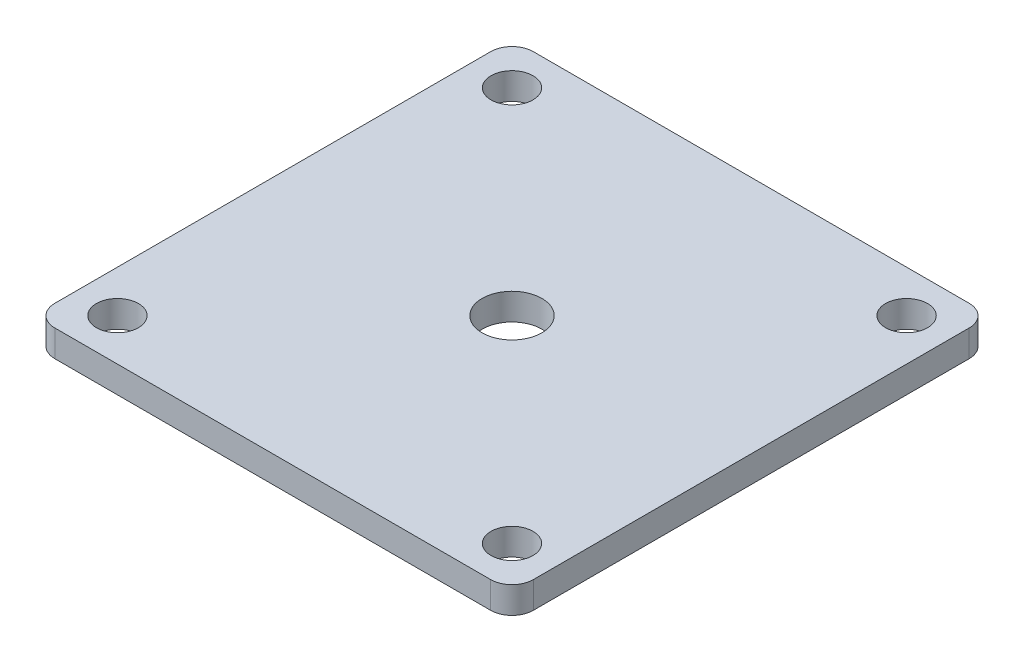
SolidWorks part; units mm, degrees
ref_plane "Front Plane" through (0, 0, 0) normal (0, 0, 1) x (1, 0, 0)
ref_plane "Top Plane" through (0, 0, 0) normal (0, 1, 0) x (1, 0, 0)
ref_plane "Right Plane" through (0, 0, 0) normal (1, 0, 0) x (0, 0, -1)
sketch "Sketch1" plane through (0, 0, 0) normal (0, 1, 0) x (1, 0, 0)
  line L0 (-13.9933, 28.5) -> (-25.96, 28.5)
  line L1 (25.96, -28.5) -> (13.9933, -28.5)
  line L2 (28.5, -25.96) -> (28.5, -13.9933)
  line L3 (25.96, 28.5) -> (13.9933, 28.5)
  line L4 (-28.5, -25.96) -> (-28.5, -13.9933)
  line L5 (28.5, -28.5) -> (-28.5, 28.5) construction
  line L6 (28.5, 28.5) -> (-28.5, -28.5) construction
  line L7 (28.5, 13.9933) -> (28.5, 25.96)
  line L8 (-13.9933, -28.5) -> (-25.96, -28.5)
  line L9 (-28.5, 13.9933) -> (-28.5, 25.96)
  line L10 (-28.5, 13.9933) -> (-28.5, -13.9933)
  line L11 (-13.9933, 28.5) -> (13.9933, 28.5)
  line L12 (28.5, 13.9933) -> (28.5, -13.9933)
  line L13 (13.9933, -28.5) -> (-13.9933, -28.5)
  circle A0 centre (0, 0) radius 3.556
  arc A5 (-25.96, -28.5) -> (-28.5, -25.96) centre (-25.96, -25.96) cw
  arc A6 (25.96, -28.5) -> (28.5, -25.96) centre (25.96, -25.96) ccw
  arc A7 (28.5, 25.96) -> (25.96, 28.5) centre (25.96, 25.96) ccw
  arc A8 (-25.96, 28.5) -> (-28.5, 25.96) centre (-25.96, 25.96) ccw
  circle A9 centre (-23.5, 23.5) radius 2.5
  circle A10 centre (23.5, 23.5) radius 2.5
  circle A11 centre (23.5, -23.5) radius 2.5
  circle A12 centre (-23.5, -23.5) radius 2.5
  point P38 (0, 0)
  dimension "D4" = 2.54
  dimension "D5" = 7.112
  dimension "D6" = 5
  dimension "D2" = 57
  dimension "D3" = 57
  dimension "D7" = 5
  dimension "D8" = 4
extrude "Boss-Extrude1" add sketch "Sketch1" along normal blind 3.175
